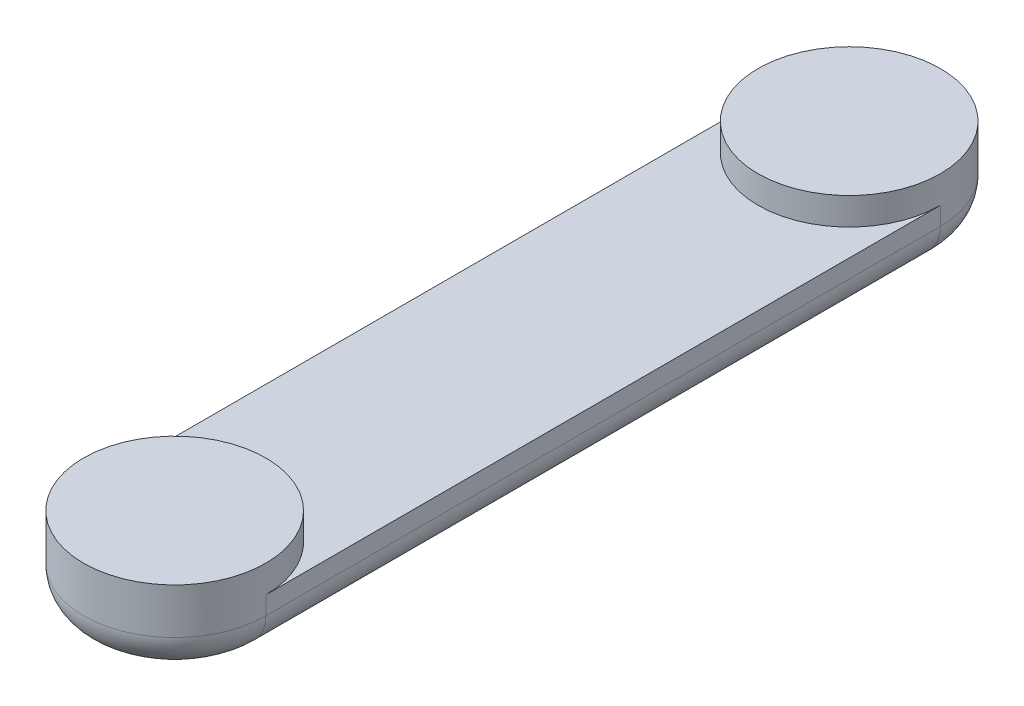
SolidWorks part; units mm, degrees
ref_plane "Front Plane" through (0, 0, 0) normal (0, 0, 1) x (1, 0, 0)
ref_plane "Top Plane" through (0, 0, 0) normal (0, 1, 0) x (1, 0, 0)
ref_plane "Right Plane" through (0, 0, 0) normal (1, 0, 0) x (0, 0, -1)
sketch "Sketch1" plane through (0, 0, 0) normal (0, 1, 0) x (1, 0, 0)
  line L0 (0, 0) -> (0, 37) construction
  line L1 (-5, 0) -> (-5, 37)
  line L2 (5, 0) -> (5, 37)
  arc A0 (-5, 0) -> (5, 0) centre (0, 0) ccw
  arc A1 (5, 37) -> (-5, 37) centre (0, 37) ccw
  point P3 (0, 18.5)
  dimension "D1" = 37
  dimension "D2" = 10
extrude "Boss-Extrude1" add sketch "Sketch1" along normal blind 3
sketch "Sketch2" plane through (0, 3, 0) normal (0, 1, 0) x (1, 0, 0)
  circle A0 centre (0, 0) radius 5
  circle A1 centre (0, 37) radius 5
  arc M1 (-5, 0) -> (5, 0) centre (0, 0) ccw
  dimension "D2" = 10
  dimension "D1" = 37
extrude "Boss-Extrude2" add sketch "Sketch2" along normal blind 1.5 contours A0 M1 | A1
fillet "Fillet1" radius 2 4 edges at (5, 0, -18.5) (0, 0, -42) (-5, 0, -18.5) (0, 0, 5)
